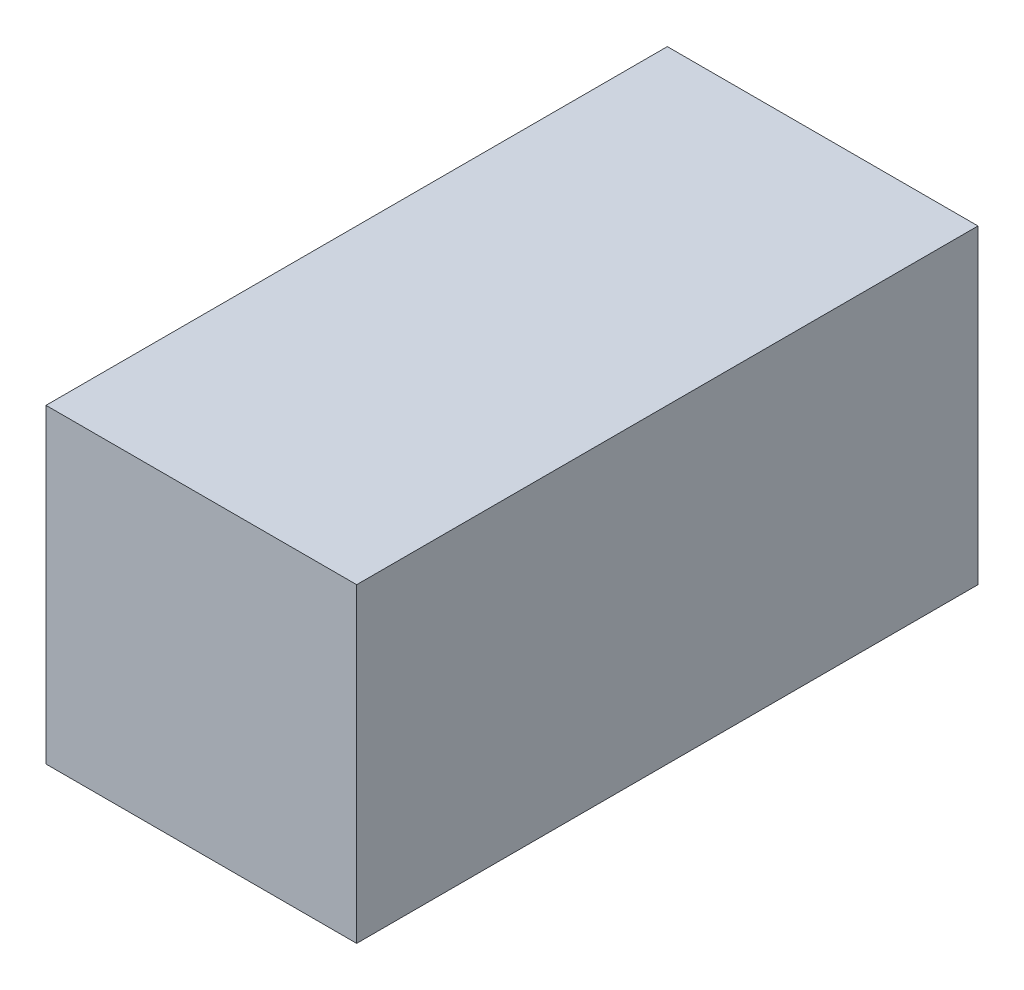
SolidWorks part; units mm, degrees
ref_plane "Front" through (0, 0, 0) normal (0, 0, 1) x (1, 0, 0)
ref_plane "Top" through (0, 0, 0) normal (0, 1, 0) x (1, 0, 0)
ref_plane "Right" through (0, 0, 0) normal (1, 0, 0) x (0, 0, -1)
sketch "Sketch1" plane through (0, 0, 0) normal (0, 0, 1) x (1, 0, 0)
  line L1 (-0.127, 0.254) -> (0.127, 0.254)
  line L2 (-0.127, 0.254) -> (-0.127, 0)
  line L3 (-0.127, 0) -> (0.127, 0)
  line L4 (0.127, 0.254) -> (0.127, 0)
  point P4 (0, 0)
  dimension "D1" = 0.254
  dimension "D2" = 0.254
extrude "Extrude1" add sketch "Sketch1" along normal mid plane 0.508
